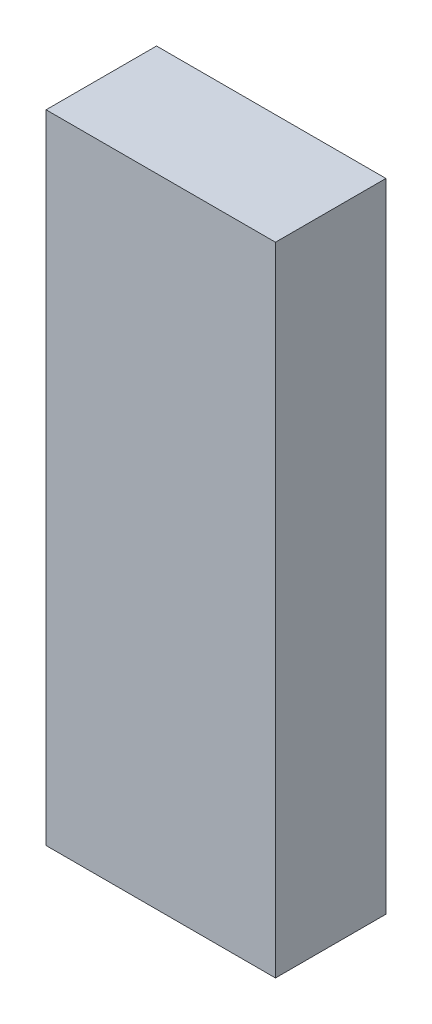
SolidWorks part; units mm, degrees
material "Hêtre"
ref_plane "Plan de face" through (0, 0, 0) normal (0, 0, 1) x (1, 0, 0)
ref_plane "Plan de dessus" through (0, 0, 0) normal (0, 1, 0) x (1, 0, 0)
ref_plane "Plan de droite" through (0, 0, 0) normal (1, 0, 0) x (0, 0, -1)
sketch "Esquisse1" plane through (0, 0, 0) normal (0, 1, 0) x (1, 0, 0)
  line L1 (0, 0) -> (27, 0)
  line L2 (0, 0) -> (0, 13)
  line L3 (0, 13) -> (27, 13)
  line L4 (27, 0) -> (27, 13)
  dimension "D1" = 27
  dimension "D2" = 13
extrude "Boss.-Extru.1" add sketch "Esquisse1" along normal blind 75
